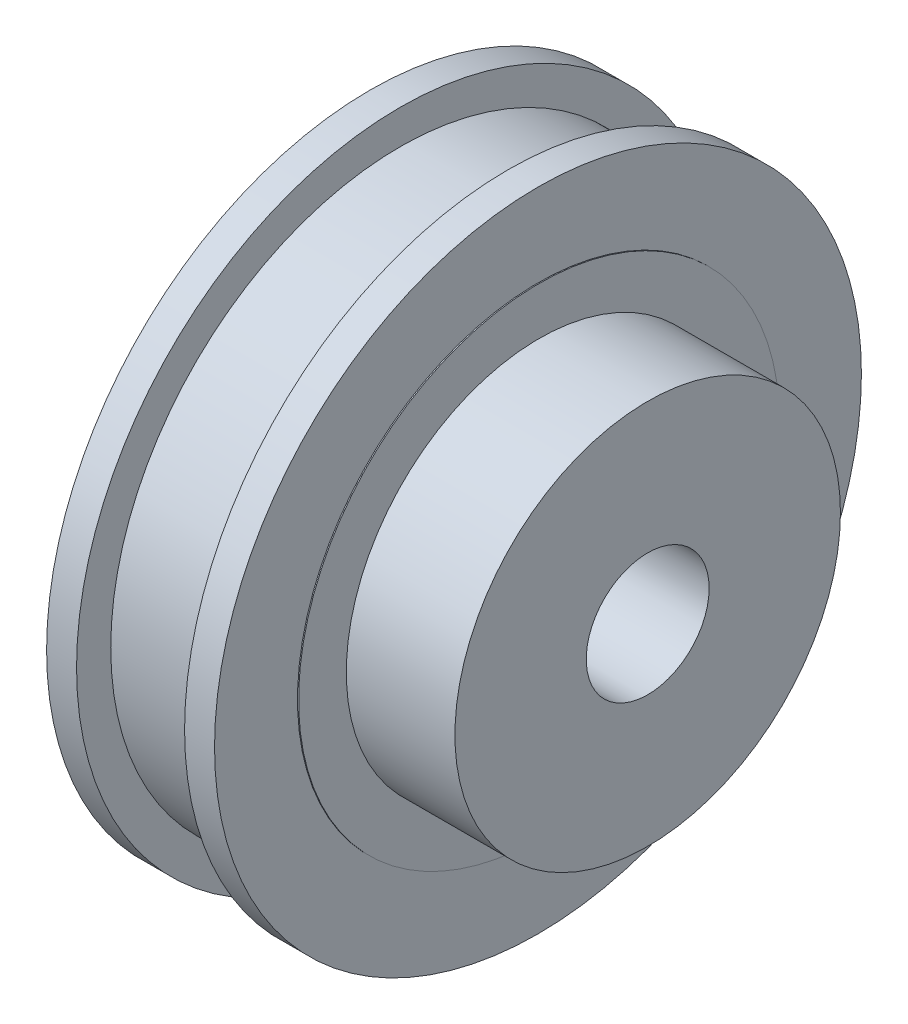
SolidWorks part; units mm, degrees
ref_plane "Front Plane" through (0, 0, 0) normal (0, 0, 1) x (1, 0, 0)
ref_plane "Top Plane" through (0, 0, 0) normal (0, 1, 0) x (1, 0, 0)
ref_plane "Right Plane" through (0, 0, 0) normal (1, 0, 0) x (0, 0, -1)
sketch "Sketch1" plane through (0, 0, 0) normal (1, 0, 0) x (0, 0, -1)
  circle A0 centre (0, 0) radius 21.05
  dimension "D1" = 42.1
extrude "Boss-Extrude1" add sketch "Sketch1" along normal blind 10.93
sketch "Sketch2" plane through (10.93, 0, 0) normal (1, 0, 0) x (0, 0, -1)
  circle A0 centre (0, 0) radius 15.65
  dimension "D1" = 31.3
extrude "Boss-Extrude2" add sketch "Sketch2" along normal blind 0.07
ref_plane "Plane2" through (5.465, 0, 0) normal (1, 0, 0) x (0, 0, -1)
mirror "Mirror1" about plane through (5.465, 0, 0) normal (1, 0, 0) of bodies 102
sketch "Sketch3" plane through (0, 0, 0) normal (0, 0, 1) x (1, 0, 0)
  line L0 (0, 0) -> (15.3362, 0) construction
  line L1 (15.3362, 18.825) -> (15.3362, -18.825) construction
  line L2 (10.93, 18.825) -> (8.98, 18.825) construction
  line L3 (10.93, -21.05) -> (10.93, 21.05) construction
  line L4 (0, 18.825) -> (1.95, 18.825) construction
  line L5 (0, 21.05) -> (0, -21.05) construction
  line L6 (10.93, 21.05) -> (0, 21.05) construction
  line L7 (1.95, 18.825) -> (8.98, 18.825)
  line L8 (1.95, 18.825) -> (1.95, 21.05)
  line L9 (1.95, 21.05) -> (8.98, 21.05)
  line L10 (8.98, 18.825) -> (8.98, 21.05)
  point P5 (15.3362, 0)
  dimension "D1" = 37.65
  dimension "D2" = 1.95
revolve "Cut-Revolve1" cut sketch "Sketch3" angle 360 about L0
sketch "Sketch5" plane through (10.93, 0, 0) normal (1, 0, 0) x (0, 0, -1)
  circle A0 centre (0, 0) radius 12.545
  dimension "D1" = 25.09
extrude "Boss-Extrude3" add sketch "Sketch5" along normal blind 7.14
sketch "Sketch6" plane through (18.07, 0, 0) normal (1, 0, 0) x (0, 0, -1)
  circle A0 centre (0, 0) radius 4
  dimension "D1" = 8
extrude "Cut-Extrude1" cut sketch "Sketch6" against normal through all
